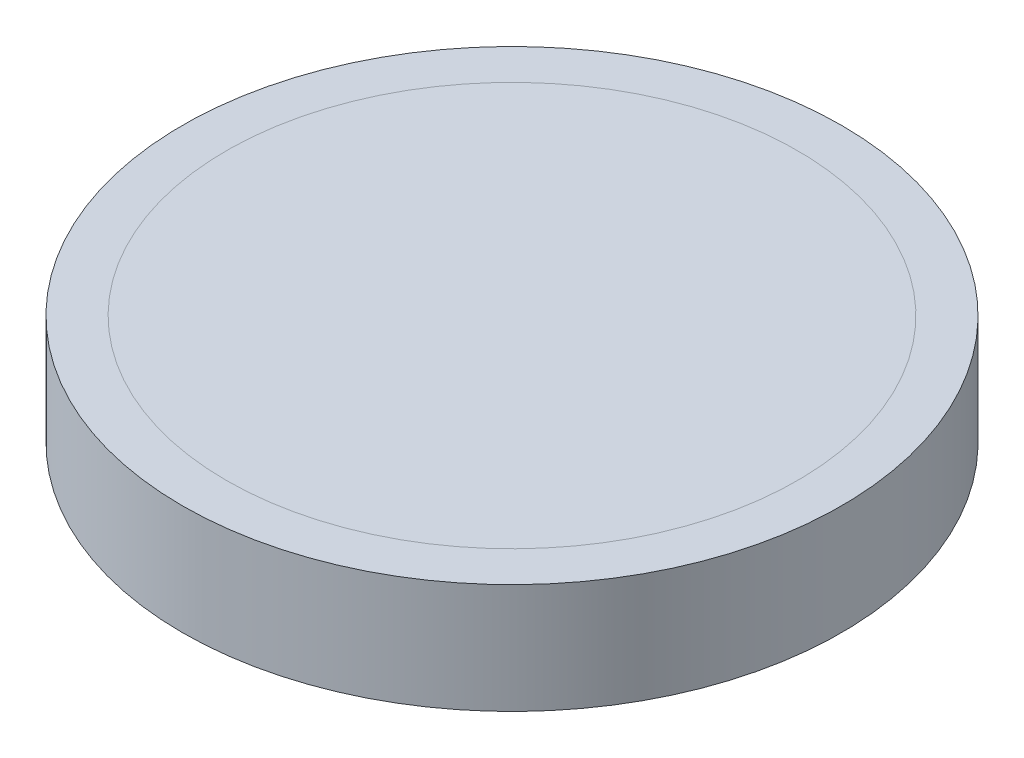
SolidWorks part; units mm, degrees
ref_plane "Front Plane" through (0, 0, 0) normal (0, 0, 1) x (1, 0, 0)
ref_plane "Top Plane" through (0, 0, 0) normal (0, 1, 0) x (1, 0, 0)
ref_plane "Right Plane" through (0, 0, 0) normal (1, 0, 0) x (0, 0, -1)
sketch "Sketch1" plane through (0, 0, 0) normal (0, 1, 0) x (1, 0, 0)
  circle A0 centre (0, 0) radius 19.05
extrude "Boss-Extrude1" add sketch "Sketch1" along normal blind 6.35
shell "Shell1" thickness 2.54
sketch "Sketch3" plane through (0, 0, 0) normal (0, -1, 0) x (1, 0, 0)
  circle A0 centre (0, 0) radius 38.1
extrude "Boss-Extrude2" [suppressed] add sketch "Sketch3" against normal blind 6.35
sketch "Sketch4" [suppressed] plane through (0, 6.35, 0) normal (0, 1, 0) x (1, 0, 0)
  circle A0 centre (18.6622, 25.6863) radius 2.54
  circle A1 centre (0, 31.75) radius 2.54
  circle A4 centre (30.196, 9.8113) radius 2.54
  circle A5 centre (30.196, -9.8113) radius 2.54
  circle A6 centre (18.6622, -25.6863) radius 2.54
  circle A7 centre (0, -31.75) radius 2.54
  circle A8 centre (-18.6622, -25.6863) radius 2.54
  circle A9 centre (-30.196, -9.8113) radius 2.54
  circle A10 centre (-30.196, 9.8113) radius 2.54
  circle A11 centre (-18.6622, 25.6863) radius 2.54
  point P25 (0, 0)
  dimension "D2" = 10
extrude "Cut-Extrude3" [suppressed] cut sketch "Sketch4" against normal blind 6.35
thread "Thread4" [suppressed] pitch 0.635 start angle 0, offset 0, length 0, pitch 0.635, diameter 5.08
ref_plane "Plane5" through (-32.736, 6.35, -9.8113) normal (0, 0, 1) x (-1, 0, 0)
sketch "Thread Profile5" plane through (-32.736, 6.35, -9.8113) normal (0, 0, 1) x (-1, 0, 0)
  line L0 (0, 0) -> (0, 0.635) construction
  line L11 (0, 0) -> (0, 0.5556)
  line L12 (0, 0.5556) -> (-0.3437, 0.3572)
  line L13 (-0.3437, 0.3572) -> (-0.3437, 0.1984)
  line L15 (-0.3437, 0.1984) -> (0, 0)
  line L17 (-0.3437, 0.2778) -> (0, 0.2778) construction
  point P2 (0, 0)
  dimension "Pitch" = 0.635
  dimension "Profile_Angle" = 60
  dimension "Profile_Land" = 0.1588
  dimension "Profile_Height" = 0.3437
thread "Thread5" [suppressed] pitch 0.635 start angle 0, offset 0, length 6.35, pitch 0.635, diameter 5.08
ref_plane "Plane6" through (-21.2022, 6.35, -25.6863) normal (0, 0, 1) x (-1, 0, 0)
sketch "Thread Profile6" plane through (-21.2022, 6.35, -25.6863) normal (0, 0, 1) x (-1, 0, 0)
  line L0 (0, 0) -> (0, 0.635) construction
  line L11 (0, 0) -> (0, 0.5556)
  line L12 (0, 0.5556) -> (-0.3437, 0.3572)
  line L13 (-0.3437, 0.3572) -> (-0.3437, 0.1984)
  line L15 (-0.3437, 0.1984) -> (0, 0)
  line L17 (-0.3437, 0.2778) -> (0, 0.2778) construction
  point P2 (0, 0)
  dimension "Pitch" = 0.635
  dimension "Profile_Angle" = 60
  dimension "Profile_Land" = 0.1588
  dimension "Profile_Height" = 0.3437
thread "Thread6" [suppressed] pitch 0.635 start angle 0, offset 0, length 6.35, pitch 0.635, diameter 5.08
ref_plane "Plane7" through (-2.54, 6.35, -31.75) normal (0, 0, 1) x (-1, 0, 0)
sketch "Thread Profile7" plane through (-2.54, 6.35, -31.75) normal (0, 0, 1) x (-1, 0, 0)
  line L0 (0, 0) -> (0, 0.635) construction
  line L11 (0, 0) -> (0, 0.5556)
  line L12 (0, 0.5556) -> (-0.3437, 0.3572)
  line L13 (-0.3437, 0.3572) -> (-0.3437, 0.1984)
  line L15 (-0.3437, 0.1984) -> (0, 0)
  line L17 (-0.3437, 0.2778) -> (0, 0.2778) construction
  point P2 (0, 0)
  dimension "Pitch" = 0.635
  dimension "Profile_Angle" = 60
  dimension "Profile_Land" = 0.1588
  dimension "Profile_Height" = 0.3437
thread "Thread7" [suppressed] pitch 0.635 start angle 0, offset 0, length 6.35, pitch 0.635, diameter 5.08
ref_plane "Plane8" through (16.1222, 6.35, -25.6863) normal (0, 0, 1) x (-1, 0, 0)
sketch "Thread Profile8" plane through (16.1222, 6.35, -25.6863) normal (0, 0, 1) x (-1, 0, 0)
  line L0 (0, 0) -> (0, 0.635) construction
  line L11 (0, 0) -> (0, 0.5556)
  line L12 (0, 0.5556) -> (-0.3437, 0.3572)
  line L13 (-0.3437, 0.3572) -> (-0.3437, 0.1984)
  line L15 (-0.3437, 0.1984) -> (0, 0)
  line L17 (-0.3437, 0.2778) -> (0, 0.2778) construction
  point P2 (0, 0)
  dimension "Pitch" = 0.635
  dimension "Profile_Angle" = 60
  dimension "Profile_Land" = 0.1588
  dimension "Profile_Height" = 0.3437
thread "Thread8" [suppressed] pitch 0.635 start angle 0, offset 0, length 6.35, pitch 0.635, diameter 5.08
ref_plane "Plane9" through (27.656, 6.35, -9.8113) normal (0, 0, 1) x (-1, 0, 0)
sketch "Thread Profile9" plane through (27.656, 6.35, -9.8113) normal (0, 0, 1) x (-1, 0, 0)
  line L0 (0, 0) -> (0, 0.635) construction
  line L11 (0, 0) -> (0, 0.5556)
  line L12 (0, 0.5556) -> (-0.3437, 0.3572)
  line L13 (-0.3437, 0.3572) -> (-0.3437, 0.1984)
  line L15 (-0.3437, 0.1984) -> (0, 0)
  line L17 (-0.3437, 0.2778) -> (0, 0.2778) construction
  point P2 (0, 0)
  dimension "Pitch" = 0.635
  dimension "Profile_Angle" = 60
  dimension "Profile_Land" = 0.1588
  dimension "Profile_Height" = 0.3437
thread "Thread9" [suppressed] pitch 0.635 start angle 0, offset 0, length 6.35, pitch 0.635, diameter 5.08
ref_plane "Plane10" through (27.656, 6.35, 9.8113) normal (0, 0, 1) x (-1, 0, 0)
sketch "Thread Profile10" plane through (27.656, 6.35, 9.8113) normal (0, 0, 1) x (-1, 0, 0)
  line L0 (0, 0) -> (0, 0.635) construction
  line L11 (0, 0) -> (0, 0.5556)
  line L12 (0, 0.5556) -> (-0.3437, 0.3572)
  line L13 (-0.3437, 0.3572) -> (-0.3437, 0.1984)
  line L15 (-0.3437, 0.1984) -> (0, 0)
  line L17 (-0.3437, 0.2778) -> (0, 0.2778) construction
  point P2 (0, 0)
  dimension "Pitch" = 0.635
  dimension "Profile_Angle" = 60
  dimension "Profile_Land" = 0.1588
  dimension "Profile_Height" = 0.3437
thread "Thread10" [suppressed] pitch 0.635 start angle 0, offset 0, length 6.35, pitch 0.635, diameter 5.08
ref_plane "Plane11" through (16.1222, 6.35, 25.6863) normal (0, 0, 1) x (-1, 0, 0)
sketch "Thread Profile11" plane through (16.1222, 6.35, 25.6863) normal (0, 0, 1) x (-1, 0, 0)
  line L0 (0, 0) -> (0, 0.635) construction
  line L11 (0, 0) -> (0, 0.5556)
  line L12 (0, 0.5556) -> (-0.3437, 0.3572)
  line L13 (-0.3437, 0.3572) -> (-0.3437, 0.1984)
  line L15 (-0.3437, 0.1984) -> (0, 0)
  line L17 (-0.3437, 0.2778) -> (0, 0.2778) construction
  point P2 (0, 0)
  dimension "Pitch" = 0.635
  dimension "Profile_Angle" = 60
  dimension "Profile_Land" = 0.1588
  dimension "Profile_Height" = 0.3437
thread "Thread11" [suppressed] pitch 0.635 start angle 0, offset 0, length 6.35, pitch 0.635, diameter 5.08
ref_plane "Plane12" through (-2.54, 6.35, 31.75) normal (0, 0, 1) x (-1, 0, 0)
sketch "Thread Profile12" plane through (-2.54, 6.35, 31.75) normal (0, 0, 1) x (-1, 0, 0)
  line L0 (0, 0) -> (0, 0.635) construction
  line L11 (0, 0) -> (0, 0.5556)
  line L12 (0, 0.5556) -> (-0.3437, 0.3572)
  line L13 (-0.3437, 0.3572) -> (-0.3437, 0.1984)
  line L15 (-0.3437, 0.1984) -> (0, 0)
  line L17 (-0.3437, 0.2778) -> (0, 0.2778) construction
  point P2 (0, 0)
  dimension "Pitch" = 0.635
  dimension "Profile_Angle" = 60
  dimension "Profile_Land" = 0.1588
  dimension "Profile_Height" = 0.3437
thread "Thread12" [suppressed] pitch 0.635 start angle 0, offset 0, length 6.35, pitch 0.635, diameter 5.08
ref_plane "Plane13" through (-21.2022, 6.35, 25.6863) normal (0, 0, 1) x (-1, 0, 0)
sketch "Thread Profile13" plane through (-21.2022, 6.35, 25.6863) normal (0, 0, 1) x (-1, 0, 0)
  line L0 (0, 0) -> (0, 0.635) construction
  line L11 (0, 0) -> (0, 0.5556)
  line L12 (0, 0.5556) -> (-0.3437, 0.3572)
  line L13 (-0.3437, 0.3572) -> (-0.3437, 0.1984)
  line L15 (-0.3437, 0.1984) -> (0, 0)
  line L17 (-0.3437, 0.2778) -> (0, 0.2778) construction
  point P2 (0, 0)
  dimension "Pitch" = 0.635
  dimension "Profile_Angle" = 60
  dimension "Profile_Land" = 0.1588
  dimension "Profile_Height" = 0.3437
thread "Thread13" [suppressed] pitch 0.635 start angle 0, offset 0, length 6.35, pitch 0.635, diameter 5.08
ref_plane "Plane14" through (-32.736, 6.35, 9.8113) normal (0, 0, 1) x (-1, 0, 0)
sketch "Thread Profile14" plane through (-32.736, 6.35, 9.8113) normal (0, 0, 1) x (-1, 0, 0)
  line L0 (0, 0) -> (0, 0.635) construction
  line L11 (0, 0) -> (0, 0.5556)
  line L12 (0, 0.5556) -> (-0.3437, 0.3572)
  line L13 (-0.3437, 0.3572) -> (-0.3437, 0.1984)
  line L15 (-0.3437, 0.1984) -> (0, 0)
  line L17 (-0.3437, 0.2778) -> (0, 0.2778) construction
  point P2 (0, 0)
  dimension "Pitch" = 0.635
  dimension "Profile_Angle" = 60
  dimension "Profile_Land" = 0.1588
  dimension "Profile_Height" = 0.3437
sketch "Sketch35" plane through (0, 6.35, 0) normal (0, 1, 0) x (1, 0, 0)
  circle A0 centre (0, 0) radius 44.45
extrude "Boss-Extrude3" add sketch "Sketch35" against normal up to next separate body
sketch "Sketch36" plane through (0, 0, 0) normal (0, -1, 0) x (1, 0, 0)
  text T0 "KLWZ"
extrude "Cut-Extrude4" cut sketch "Sketch36" against normal blind 1.27
